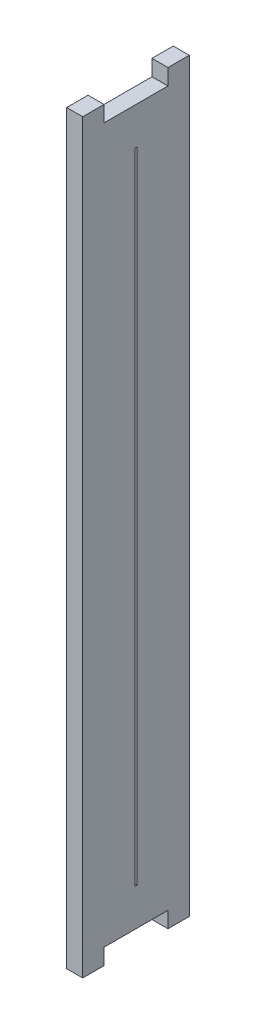
SolidWorks part; units mm, degrees
ref_plane "Front Plane" through (0, 0, 0) normal (0, 0, 1) x (1, 0, 0)
ref_plane "Top Plane" through (0, 0, 0) normal (0, 1, 0) x (1, 0, 0)
ref_plane "Right Plane" through (0, 0, 0) normal (1, 0, 0) x (0, 0, -1)
sketch "Sketch1" plane through (0, 0, 0) normal (1, 0, 0) x (0, 0, -1)
  line L1 (-10, -30.8442) -> (0, -30.8442)
  line L2 (-10, -30.8442) -> (-10, 39.1558)
  line L3 (-10, 39.1558) -> (0, 39.1558)
  line L4 (0, -30.8442) -> (0, 39.1558)
  dimension "D1" = 70
  dimension "D2" = 10
extrude "Boss-Extrude1" add sketch "Sketch1" along normal blind 1.5
sketch "Sketch3" plane through (1.5, 0, 0) normal (1, 0, 0) x (0, 0, -1)
  line L1 (-5.1, 34.1558) -> (-4.9, 34.1558)
  line L2 (-5.1, 34.1558) -> (-5.1, -25.8442)
  line L3 (-5.1, -25.8442) -> (-4.9, -25.8442)
  line L4 (-4.9, 34.1558) -> (-4.9, -25.8442)
  line L6 (-10, 39.1558) -> (-10, -30.8442) construction
  line L7 (0, -30.8442) -> (0, 39.1558) construction
  line L8 (-10, -30.8442) -> (0, -30.8442) construction
  line L9 (0, 39.1558) -> (-10, 39.1558) construction
  dimension "D1" = 4.9
  dimension "D2" = 4.9
  dimension "D3" = 5
  dimension "D4" = 5
extrude "Cut-Extrude2" cut sketch "Sketch3" against normal blind 10
sketch "Sketch4" plane through (1.5, 0, 0) normal (1, 0, 0) x (0, 0, -1)
  line L0 (0, 39.1558) -> (-10, 39.1558) construction
  line L1 (-8, 39.1558) -> (-2, 39.1558)
  line L2 (-8, 39.1558) -> (-8, 37.6558)
  line L3 (-8, 37.6558) -> (-2, 37.6558)
  line L4 (-2, 39.1558) -> (-2, 37.6558)
  line L5 (-10, -30.8442) -> (0, -30.8442) construction
  line L6 (-8, -30.8442) -> (-2, -30.8442)
  line L7 (-8, -30.8442) -> (-8, -29.3442)
  line L8 (-8, -29.3442) -> (-2, -29.3442)
  line L9 (-2, -30.8442) -> (-2, -29.3442)
  line L10 (-10, 39.1558) -> (-10, -30.8442) construction
  line L11 (0, -30.8442) -> (0, 39.1558) construction
  dimension "D1" = 1.5
  dimension "D2" = 2
  dimension "D3" = 2
  dimension "D4" = 2
extrude "Cut-Extrude3" cut sketch "Sketch4" against normal blind 10
